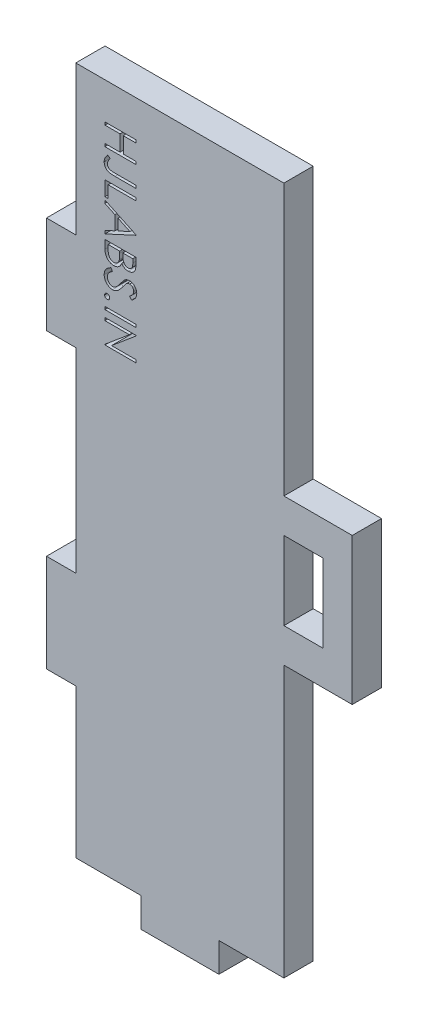
SolidWorks part; units mm, degrees
ref_plane "Front Plane" through (0, 0, 0) normal (0, 0, 1) x (1, 0, 0)
ref_plane "Top Plane" through (0, 0, 0) normal (0, 1, 0) x (1, 0, 0)
ref_plane "Right Plane" through (0, 0, 0) normal (1, 0, 0) x (0, 0, -1)
sketch "Sketch1" plane through (0, 0, 0) normal (0, 0, 1) x (1, 0, 0)
  line L5 (3, -29) -> (-24.3118, 47.5) construction
  line L6 (3, 47.5) -> (-24.3118, -29) construction
  line L7 (3, -10.75) -> (0, -10.75) construction
  line L10 (3, -0.75) -> (0, -0.75) construction
  line L12 (3, 19.25) -> (0, 19.25) construction
  line L13 (3, 29.25) -> (0, 29.25) construction
  line L25 (-10.6559, -35.4999) -> (-10.6559, 53.9999) construction
  line L27 (-24.3118, 19.25) -> (-21.3118, 19.25)
  line L28 (-24.3118, 29.25) -> (-21.3118, 29.25)
  line L29 (-24.3118, -0.75) -> (-21.3118, -0.75)
  line L30 (-24.3118, -10.75) -> (-21.3118, -10.75)
  line L31 (-24.3118, -10.75) -> (-24.3118, -0.75)
  line L32 (-21.3118, -10.75) -> (-21.3118, -26)
  line L33 (-21.3118, -0.75) -> (-21.3118, 19.25)
  line L34 (-21.3118, 29.25) -> (-21.3118, 44.5)
  line L35 (-24.3118, 19.25) -> (-24.3118, 29.25)
  line L43 (-2, 44.5) -> (0, 44.5) construction
  line L44 (-19.3118, 44.5) -> (-2, 44.5) construction
  line L45 (-21.3118, 44.5) -> (-19.3118, 44.5) construction
  line L47 (0, -26) -> (0, 1.75)
  line L48 (-21.3118, 9.25) -> (16.8002, 9.25) construction
  line L49 (-2, 44.5) -> (0, 44.5)
  line L50 (-19.3118, 44.5) -> (-2, 44.5)
  line L51 (-21.3118, 44.5) -> (-19.3118, 44.5)
  line L52 (0, -26) -> (-2, -26)
  line L53 (-19.3118, -26) -> (-21.3118, -26)
  line L54 (-19.3118, -26) -> (-2, -26)
  line L55 (0, 16.75) -> (0, 44.5)
  line L56 (0, 1.75) -> (7, 1.75)
  line L58 (0, 16.75) -> (7, 16.75)
  line L59 (7, 1.75) -> (7, 16.75)
  line L60 (0, 1.75) -> (7, 16.75) construction
  line L61 (0, 16.75) -> (7, 1.75) construction
  line L62 (0, 16.75) -> (0, 1.75) construction
  line L64 (0, 5.25) -> (4, 5.25)
  line L65 (0, 5.25) -> (0, 13.25)
  line L66 (0, 13.25) -> (4, 13.25)
  line L67 (4, 5.25) -> (4, 13.25)
  line L68 (0, 5.25) -> (4, 13.25) construction
  line L69 (0, 13.25) -> (4, 5.25) construction
  point P4 (-10.6559, 9.25)
  point P18 (-10.6559, 9.25)
  point P32 (3.5, 9.25)
  point P41 (2, 9.25)
  dimension "D1" = 7
  dimension "D2" = 15
  dimension "D3" = 4
  dimension "D4" = 8
extrude "Boss-Extrude1" add sketch "Sketch1" along normal blind 3
sketch "Sketch6" plane through (0, 0, 3) normal (0, 0, 1) x (1, 0, 0)
  line L0 (-18.3216, 41.1695) -> (-18.3216, -20.0325) construction
  text T0 "HJLABS.IN"
extrude "Cut-Extrude2" cut sketch "Sketch6" against normal blind 3
sketch "Sketch7" plane through (0, 0, 3) normal (0, 0, 1) x (1, 0, 0)
  line L0 (-14.6559, -26) -> (-14.6559, -29) construction
  line L1 (-6.6559, -26) -> (-6.6559, -29) construction
  line L2 (-14.6559, -26) -> (-14.6559, -29)
  line L3 (-6.6559, -26) -> (-6.6559, -29)
  line L4 (-6.6559, -26) -> (-14.6559, -26)
  line L5 (-6.6559, -29) -> (-14.6559, -29)
extrude "Boss-Extrude2" add sketch "Sketch7" against normal blind 3
